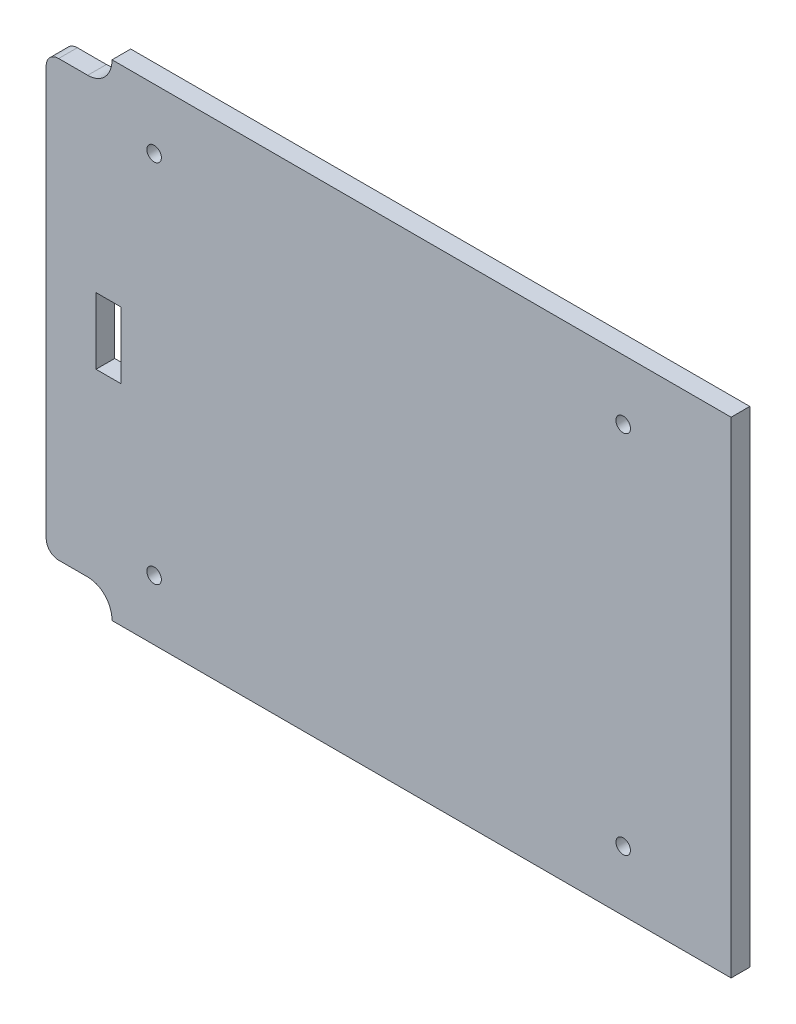
SolidWorks part; units mm, degrees
material "ABS"
ref_plane "Front Plane" through (0, 0, 0) normal (0, 0, 1) x (1, 0, 0)
ref_plane "Top Plane" through (0, 0, 0) normal (0, 1, 0) x (1, 0, 0)
ref_plane "Right Plane" through (0, 0, 0) normal (1, 0, 0) x (0, 0, -1)
sketch "Sketch2" plane through (0, 0, 0) normal (0, 0, 1) x (1, 0, 0)
  line L1 (82.5, -58.5) -> (-82.5, -58.5)
  line L2 (82.5, -58.5) -> (82.5, 58.5)
  line L3 (82.5, 58.5) -> (-82.5, 58.5)
  line L4 (-82.5, -58.5) -> (-82.5, 58.5)
  line L5 (82.5, -58.5) -> (-82.5, 58.5) construction
  line L6 (82.5, 58.5) -> (-82.5, -58.5) construction
  point P0 (0, 0)
  dimension "D1" = 117
  dimension "D2" = 165
extrude "Boss-Extrude1" add sketch "Sketch2" along normal blind 4.5
sketch "Sketch3" plane through (0, 0, 4.5) normal (0, 0, 1) x (1, 0, 0)
  line L0 (82.5, 58.5) -> (-82.5, 58.5) construction
  line L1 (-82.5, 58.5) -> (-82.5, -58.5) construction
  circle A0 centre (-56.5, 44) radius 1.75
  dimension "D1" = 3.5
  dimension "D2" = 14.5
  dimension "D3" = 26
extrude "Cut-Extrude1" cut sketch "Sketch3" against normal through all contours A0
mirror "Mirror1" about plane through (0, 0, 0) normal (1, 0, 0) of "Cut-Extrude1"
mirror "Mirror2" about plane through (0, 0, 0) normal (0, 1, 0) of "Mirror1", "Cut-Extrude1"
sketch "Sketch4" plane through (0, 0, 4.5) normal (0, 0, 1) x (1, 0, 0)
  line L0 (0, 0) -> (-82.5, 0) construction
  line L6 (-82.5, 58.5) -> (-82.5, -58.5) construction
  line L8 (-64.5, -8) -> (-70.5, -8)
  line L9 (-64.5, -8) -> (-64.5, 8)
  line L10 (-64.5, 8) -> (-70.5, 8)
  line L11 (-70.5, -8) -> (-70.5, 8)
  line L12 (-64.5, -8) -> (-70.5, 8) construction
  line L13 (-64.5, 8) -> (-70.5, -8) construction
  point P4 (-67.5, 0)
  dimension "D1" = 6
  dimension "D2" = 16
  dimension "D3" = 15
extrude "Cut-Extrude2" cut sketch "Sketch4" against normal up to next
sketch "Sketch5" plane through (0, 0, 4.5) normal (0, 0, 1) x (1, 0, 0)
  line L0 (-82.5, 47.2345) -> (-82.5, 49.34)
  line L1 (-82.5, 58.5) -> (-82.5, -58.5) construction
  line L2 (-79.5016, 52.3384) -> (-72.4926, 52.3384)
  line L3 (82.5, 58.5) -> (-82.5, 58.5) construction
  line L4 (-66.6411, 58.5) -> (-82.5, 58.5)
  line L5 (-82.5, 58.5) -> (-82.5, 47.2345)
  line L6 (-64.5, -8) -> (-64.5, 8) construction
  line L7 (-64.5, 8) -> (-70.5, 8) construction
  arc A0 (-82.5, 49.34) -> (-79.5016, 52.3384) centre (-79.5016, 49.34) cw
  arc A1 (-72.4926, 52.3384) -> (-67.3792, 55.4561) centre (-72.4926, 58.0907) ccw
  arc A2 (-67.3792, 55.4561) -> (-66.6411, 58.5) centre (-73.2871, 58.5) ccw
  line M9 (-82.5, 58.5) -> (-82.5, -58.5)
  line M12 (82.5, 58.5) -> (-82.5, 58.5)
  dimension "D1" = 2.9984
  dimension "D2" = 5.7523
  dimension "D3" = 6.646
  dimension "D4" = 2.1411
  dimension "D5" = 2.8792
  dimension "D6" = 39.2345
extrude "Cut-Extrude3" cut sketch "Sketch5" against normal up to next (4.5 mm away) contours A1 A2 A0 L2 M12 M9
mirror "Mirror3" about plane through (0, 0, 0) normal (0, 1, 0) of "Cut-Extrude3"
